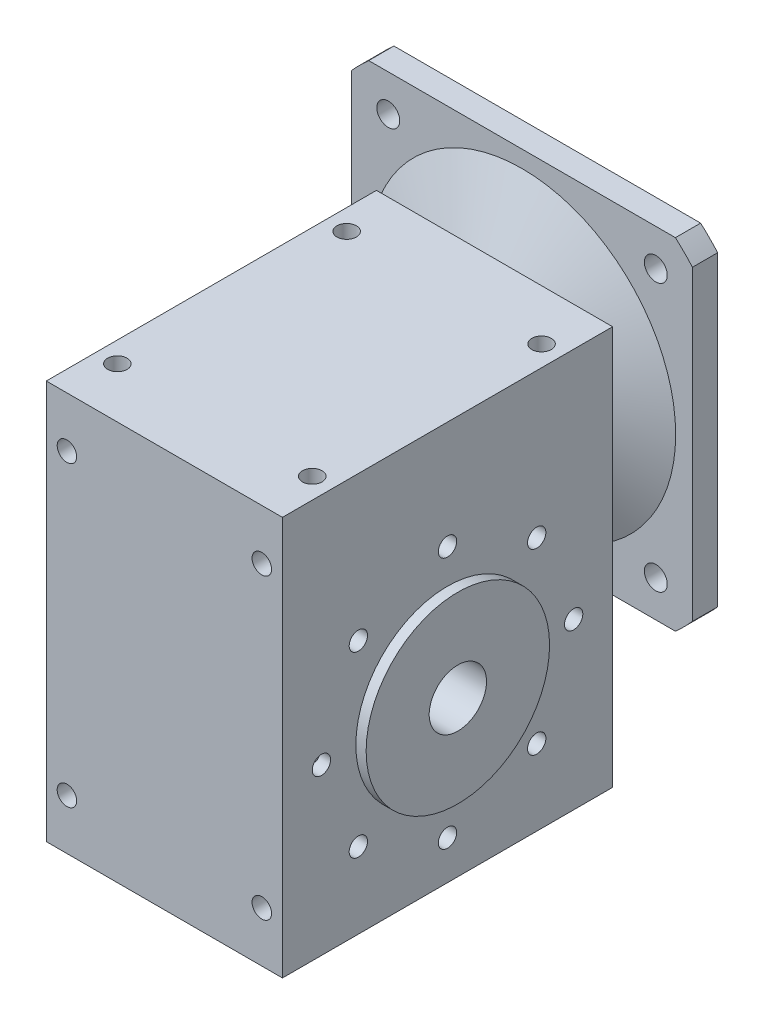
SolidWorks part; units mm, degrees
material "1060 Сплав"
ref_plane "Спереди" through (0, 0, 0) normal (0, 0, 1) x (1, 0, 0)
ref_plane "Сверху" through (0, 0, 0) normal (0, 1, 0) x (1, 0, 0)
ref_plane "Справа" through (0, 0, 0) normal (1, 0, 0) x (0, 0, -1)
sketch "Эскиз1" plane through (0, 0, 0) normal (0, 1, 0) x (1, 0, 0)
  line L0 (0, 0) -> (0, 72) construction
  line L1 (-51.5, 72) -> (51.5, 72)
  line L2 (-51.5, 72) -> (-51.5, -72)
  line L3 (-51.5, -72) -> (51.5, -72)
  line L4 (51.5, 72) -> (51.5, -72)
  line L5 (0, 0) -> (51.5, 0) construction
  point P7 (51.5, 0)
  point P10 (0, 72)
  dimension "D1" = 103
  dimension "D2" = 144
extrude "Бобышка-Вытянуть1" add sketch "Эскиз1" along normal blind 174
sketch "Эскиз2" plane through (0, 0, 72) normal (0, 0, 1) x (1, 0, 0)
  line L0 (-109.3819, 72) -> (115.1187, 72) construction
  line L1 (-51.5, 0) -> (51.5, 0) construction
  dimension "D1" = 72
sketch "Эскиз3" plane through (51.5, 0, 0) normal (1, 0, 0) x (0, 0, -1)
  line L0 (-72, 72) -> (72, 72) construction
  line L1 (-72, 0) -> (72, 0) construction
  line L2 (-72, 174) -> (-72, 0) construction
  line L3 (72, 174) -> (72, 0) construction
  circle A0 centre (0, 72) radius 12.5
  dimension "D2" = 25
  dimension "D1" = 72
extrude "Вырез-Вытянуть1" cut sketch "Эскиз3" against normal through all
sketch "Эскиз4" plane through (51.5, 0, 0) normal (1, 0, 0) x (0, 0, -1)
  line L0 (0, 72) -> (0, 127) construction
  circle A1 centre (0, 127) radius 4
  circle A2 centre (38.8909, 110.8909) radius 4
  circle A3 centre (55, 72) radius 4
  circle A4 centre (38.8909, 33.1091) radius 4
  circle A5 centre (0, 17) radius 4
  circle A6 centre (-38.8909, 33.1091) radius 4
  circle A7 centre (-55, 72) radius 4
  circle A8 centre (-38.8909, 110.8909) radius 4
  point P22 (0, 72)
  dimension "D2" = 8
  dimension "D1" = 55
  dimension "D3" = 8
extrude "Вырез-Вытянуть2" cut sketch "Эскиз4" against normal through all
sketch "Эскиз5" plane through (0, 174, 0) normal (0, 1, 0) x (1, 0, 0)
  line L0 (0, 72) -> (0, -65.0127) construction
  line L1 (-42.5, 50) -> (42.5, 50) construction
  line L2 (-42.5, 50) -> (-42.5, -50) construction
  line L3 (-42.5, -50) -> (42.5, -50) construction
  line L4 (42.5, 50) -> (42.5, -50) construction
  line L5 (51.5, 72) -> (-51.5, 72) construction
  line L6 (-51.5, 0) -> (51.5, 0) construction
  line L7 (-51.5, 72) -> (-51.5, -72) construction
  line L8 (51.5, -72) -> (51.5, 72) construction
  circle A0 centre (-42.5, 50) radius 4.25
  circle A1 centre (42.5, 50) radius 4.25
  circle A2 centre (42.5, -50) radius 4.25
  circle A3 centre (-42.5, -50) radius 4.25
  point P15 (-42.5, 0)
  point P16 (0, -50)
  dimension "D3" = 8.5
  dimension "D1" = 85
  dimension "D2" = 100
extrude "Вырез-Вытянуть3" cut sketch "Эскиз5" against normal through all
ref_plane "Плоскость1" through (0, 0, 0) normal (1, 0, 0) x (0, 0, -1)
sketch "Эскиз6" plane through (0, 0, 0) normal (1, 0, 0) x (0, 0, -1)
  line L0 (89, 146) -> (72, 146)
  line L1 (72, 146) -> (72, 174)
  line L2 (72, 174) -> (84, 202)
  line L3 (84, 202) -> (84, 235)
  line L4 (84, 235) -> (95, 235)
  line L5 (95, 235) -> (95, 200)
  line L6 (95, 200) -> (89, 200)
  line L8 (79, 152.5) -> (89, 152.5)
  line L9 (89, 152.5) -> (89, 146)
  line L10 (-119.058, 135) -> (159.0244, 135) construction
  line L11 (-72, 0) -> (72, 0) construction
  line L12 (-72, 174) -> (72, 174) construction
  line L13 (72, 174) -> (72, 0) construction
  line L14 (79, 152.5) -> (79, 176.6667)
  line L15 (79, 176.6667) -> (89, 200)
  point P16 (0, 174)
  dimension "D1" = 135
  dimension "D2" = 95
  dimension "D3" = 200
  dimension "D4" = 130
  dimension "D5" = 22
  dimension "D6" = 10
  dimension "D8" = 11
  dimension "D9" = 35
  dimension "D10" = 33
  dimension "D7" = 6
  dimension "D11" = 6
  dimension "D12" = 6
revolve "Повернуть1" add sketch "Эскиз6" angle 360 about L10
sketch "Эскиз7" plane through (0, 0, 0) normal (0, -1, 0) x (1, 0, 0)
  line L1 (-35, -70) -> (35, -70)
  line L2 (-35, -70) -> (-35, 70)
  line L3 (-35, 70) -> (35, 70)
  line L4 (35, -70) -> (35, 70)
  line L5 (-35, -70) -> (35, 70) construction
  line L6 (-35, 70) -> (35, -70) construction
  point P0 (0, 0)
  dimension "D1" = 70
  dimension "D2" = 140
extrude "Вырез-Вытянуть4" cut sketch "Эскиз7" against normal blind 169
sketch "Эскиз8" plane through (0, 0, 0) normal (1, 0, 0) x (0, 0, -1)
  circle A0 centre (0, 72) radius 40
  circle A1 centre (0, 72) radius 12.5
  dimension "D1" = 80
extrude "Бобышка-Вытянуть2" add sketch "Эскиз8" along normal mid plane 112
sketch "Эскиз9" plane through (0, 0, 72) normal (0, 0, 1) x (1, 0, 0)
  line L0 (-42.5, 152) -> (42.5, 152) construction
  line L1 (-42.5, 22) -> (-42.5, 152) construction
  line L2 (51.5, 174) -> (51.5, 0) construction
  line L3 (-51.5, 174) -> (51.5, 174) construction
  line L4 (-51.5, 0) -> (51.5, 0) construction
  circle A0 centre (-42.5, 152) radius 4.25
  circle A1 centre (42.5, 152) radius 4.25
  circle A2 centre (42.5, 22) radius 4.25
  circle A3 centre (-42.5, 22) radius 4.25
  point P8 (0, 152)
  point P11 (51.5, 87)
  point P12 (-42.5, 87)
  dimension "D1" = 85
  dimension "D3" = 8.5
  dimension "D2" = 130
  dimension "D4" = 22
  dimension "D5" = 22
extrude "Вырез-Вытянуть5" cut sketch "Эскиз9" against normal up to surface (144 mm away) up to face at (6.5, 109.5, -72)
sketch "Эскиз10" plane through (0, 0, -95) normal (0, 0, -1) x (-1, 0, 0)
  line L0 (-58.3363, 193.3363) -> (0, 135) construction
  line L1 (0, 135) -> (0, 0) construction
  circle A0 centre (-58.3363, 193.3363) radius 5
  circle A1 centre (58.3363, 193.3363) radius 5
  circle A2 centre (58.3363, 76.6637) radius 5
  circle A3 centre (-58.3363, 76.6637) radius 5
  point P15 (0, 135)
  dimension "D1" = 45
  dimension "D3" = 10
  dimension "D2" = 82.5
  dimension "D4" = 4
extrude "Вырез-Вытянуть6" cut sketch "Эскиз10" against normal blind 17
sketch "Эскиз11" plane through (0, 0, -95) normal (0, 0, -1) x (-1, 0, 0)
  line L1 (74.3363, 209.3363) -> (-74.3363, 209.3363)
  line L2 (74.3363, 209.3363) -> (74.3363, 60.6637)
  line L3 (74.3363, 60.6637) -> (-74.3363, 60.6637)
  line L4 (-74.3363, 209.3363) -> (-74.3363, 60.6637)
  line L5 (74.3363, 209.3363) -> (-74.3363, 60.6637) construction
  line L6 (74.3363, 60.6637) -> (-74.3363, 209.3363) construction
  circle A4 centre (58.3363, 193.3363) radius 5 construction
  circle A8 centre (58.3363, 76.6637) radius 5 construction
  point P0 (0, 135)
  dimension "D1" = 11
  dimension "D2" = 11
  dimension "D3" = 11
extrude "Вырез-Вытянуть7" cut sketch "Эскиз11" against normal blind 17 flip side to cut
sketch "Эскиз14" plane through (0, 0, -89) normal (0, 0, -1) x (-1, 0, 0)
  circle A0 centre (0, 135) radius 17.5 construction
  circle A1 centre (0, 135) radius 17.5
extrude "Бобышка-Вытянуть3" add sketch "Эскиз14" against normal blind 54
sketch "Эскиз12" plane through (0, 0, -89) normal (0, 0, -1) x (-1, 0, 0)
  circle A1 centre (0, 135) radius 11
  circle A2 centre (0, 135) radius 17.5 construction
  dimension "D1" = 22
extrude "Вырез-Вытянуть8" cut sketch "Эскиз12" against normal blind 52
equation "\"D1@Эскиз6\"=72+63"
